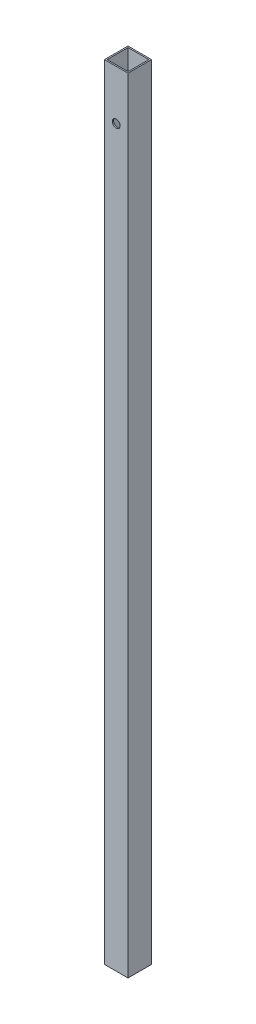
SolidWorks part; units mm, degrees
ref_plane "Front Plane" through (0, 0, 0) normal (0, 0, 1) x (1, 0, 0)
ref_plane "Top Plane" through (0, 0, 0) normal (0, 1, 0) x (1, 0, 0)
ref_plane "Right Plane" through (0, 0, 0) normal (1, 0, 0) x (0, 0, -1)
sketch "Sketch1" plane through (0, 0, 0) normal (0, 1, 0) x (1, 0, 0)
  line L0 (-8, 8) -> (-8, -8)
  line L1 (-9, 9) -> (9, 9)
  line L2 (-9, 9) -> (-9, -9)
  line L3 (-9, -9) -> (9, -9)
  line L4 (9, 9) -> (9, -9)
  line L5 (-9, 9) -> (9, -9) construction
  line L6 (-9, -9) -> (9, 9) construction
  line L7 (-8, -8) -> (8, -8)
  line L8 (8, 8) -> (8, -8)
  line L9 (-8, 8) -> (8, 8)
  point P0 (0, 0)
  dimension "D1" = 18
  dimension "D2" = 18
  dimension "D3" = 1
extrude "Boss-Extrude1" add sketch "Sketch1" along normal blind 600
sketch "Sketch2" plane through (0, 0, 9) normal (0, 0, 1) x (1, 0, 0)
  line L0 (-9, 600) -> (9, 600) construction
  line L1 (-9, 600) -> (-9, 0) construction
  circle A0 centre (0, 562) radius 3
  dimension "D1" = 6
  dimension "D2" = 38
  dimension "D3" = 9
extrude "Cut-Extrude1" cut sketch "Sketch2" against normal blind 993
